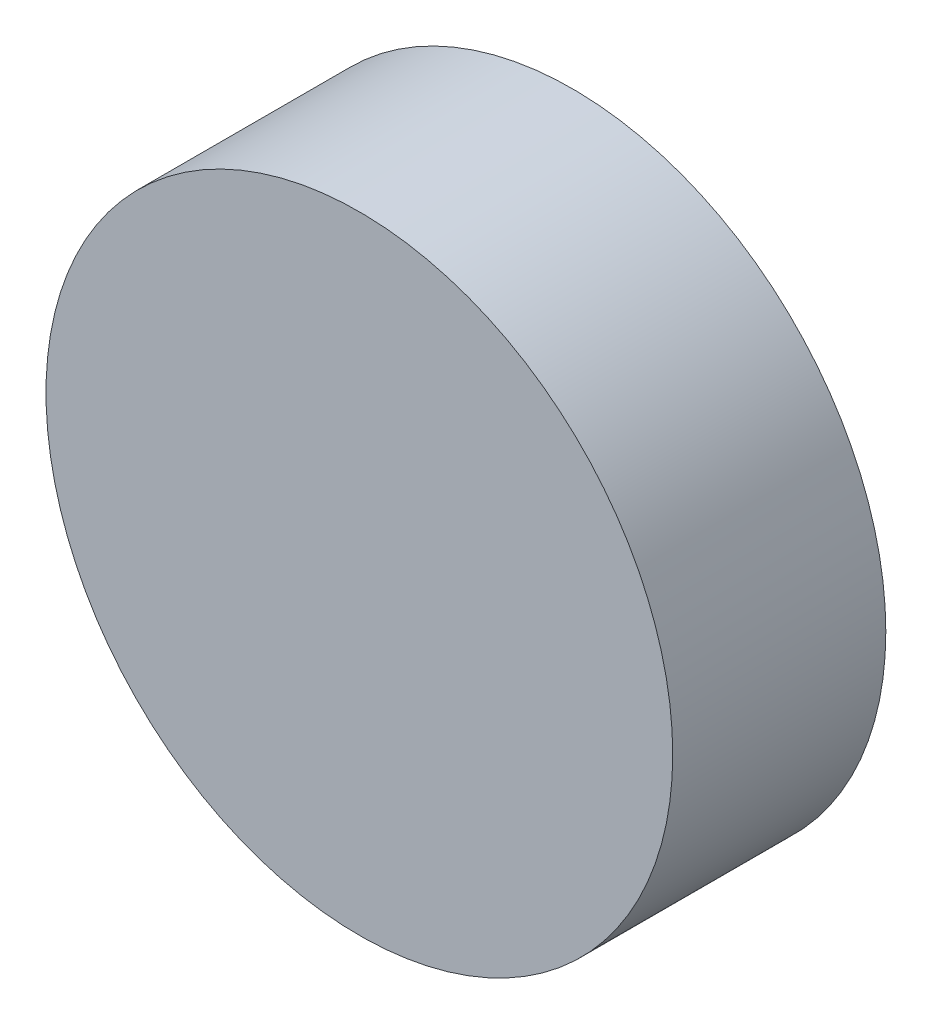
SolidWorks part; units mm, degrees
ref_plane "Front Plane" through (0, 0, 0) normal (0, 0, 1) x (1, 0, 0)
ref_plane "Top Plane" through (0, 0, 0) normal (0, 1, 0) x (1, 0, 0)
ref_plane "Right Plane" through (0, 0, 0) normal (1, 0, 0) x (0, 0, -1)
sketch "Sketch1" plane through (0, 0, 0) normal (0, 0, 1) x (1, 0, 0)
  circle A0 centre (0, 0) radius 25
  dimension "D1" = 50
extrude "Boss-Extrude1" add sketch "Sketch1" along normal blind 17
hole_wizard "Ø3.0mm Dowel Hole1" positions "Sketch11" profile "Sketch12" hole size "Ø3.0" standard "ANSI Metric"
sketch "Sketch11" plane through (0, 0, 0) normal (0, 0, -1) x (-1, 0, 0)
  point P0 (0, 21)
  dimension "D1" = 21
sketch "Sketch12" plane through (0, 21, 0) normal (1, 0, 0) x (0, 1, 0)
  line L0 (0, 0) -> (0, 5.9013)
  line L1 (0, 5.9013) -> (1.5, 5)
  line L2 (1.5, 5) -> (1.5, 0)
  line L5 (1.5, 0) -> (0, 0)
  line L10 (0, 5.9013) -> (-1.5, 5) construction
  line L11 (0, -6.35) -> (0, 107.95) construction
  dimension "Hole Dia." = 3
  dimension "Hole Depth" = 5
  dimension "Drill Angle" = 118
pattern_circular "CirPattern1" count 3 over 360 about axis through (0, 0, 0) along (0, 0, 1) of "Ø3.0mm Dowel Hole1"
ref_plane "Plane1" through (0, -25, 0) normal (0, -1, 0) x (-1, 0, 0)
sketch "Sketch14" plane through (0, -25, 0) normal (0, -1, 0) x (-1, 0, 0)
  line L1 (-8.6674, -1.3979) -> (6.9824, -1.3979)
  line L2 (-8.6674, -1.3979) -> (-8.6674, -15.3979)
  line L3 (-8.6674, -15.3979) -> (6.9824, -15.3979)
  line L4 (6.9824, -1.3979) -> (6.9824, -15.3979)
  line L5 (-8.6674, -1.3979) -> (6.9824, -15.3979) construction
  line L6 (-8.6674, -15.3979) -> (6.9824, -1.3979) construction
  point P0 (-0.8425, -8.3979)
  point P5 (0, 0)
  point P6 (0, -2.7731)
  point P7 (0, -7.3505)
  point P8 (0, -8.4616)
  point P9 (-0.8425, -8.3979)
  dimension "D1" = 15.6499
  dimension "D2" = 14
extrude "Cut-Extrude2" cut sketch "Sketch14" against normal blind 17.25
sketch "Sketch15" plane through (0, 0, 0) normal (0, 0, -1) x (-1, 0, 0)
  arc A0 (-3.9818, 20.619) -> (3.9818, 20.619) centre (0, 21) ccw
  arc A1 (-15.8657, -13.7579) -> (-19.8475, -6.8612) centre (-18.1865, -10.5) ccw
  arc A2 (19.8475, -6.8612) -> (15.8657, -13.7579) centre (18.1865, -10.5) ccw
  arc A3 (-3.9818, 20.619) -> (-19.8475, -6.8612) centre (0, 0) ccw
  arc A4 (19.8475, -6.8612) -> (3.9818, 20.619) centre (0, 0) ccw
  arc A5 (-15.8657, -13.7579) -> (15.8657, -13.7579) centre (0, 0) ccw
  dimension "D1" = 8
  dimension "D2" = 8
  dimension "D3" = 8
extrude "Cut-Extrude3" cut sketch "Sketch15" against normal blind 15
sketch "Sketch16" plane through (0, 0, 15) normal (0, 0, -1) x (-1, 0, 0)
  line L0 (0, 0) -> (0, 14.2598) construction
  circle A0 centre (-7, 8.0388) radius 2
  circle A1 centre (-7, 8.0388) radius 1
  circle A2 centre (7, 8.0388) radius 1
  circle A3 centre (7, 8.0388) radius 2
  dimension "D2" = 4
  dimension "D3" = 2
  dimension "D1" = 7
extrude "Boss-Extrude2" add sketch "Sketch16" along normal blind 3
